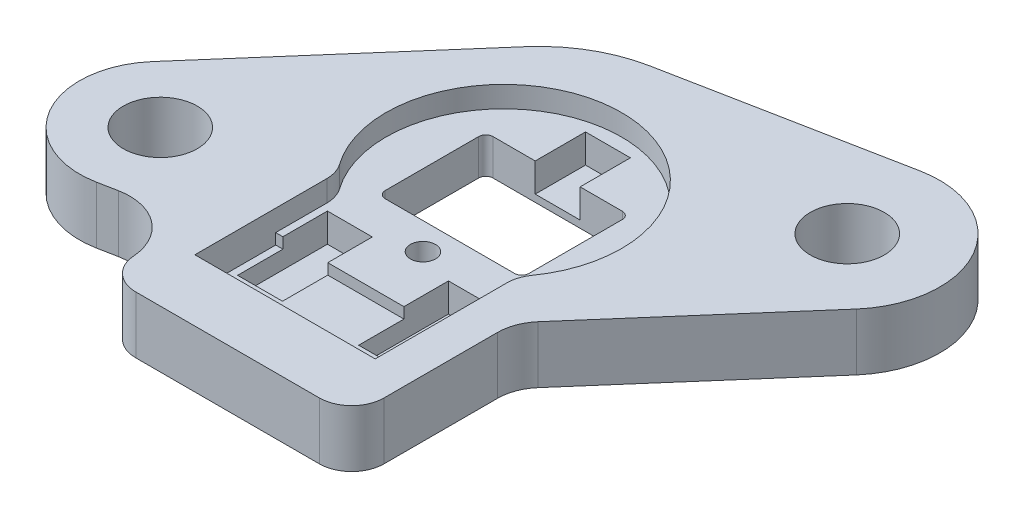
SolidWorks part; units mm, degrees
ref_plane "Front Plane" through (0, 0, 0) normal (0, 0, 1) x (1, 0, 0)
ref_plane "Top Plane" through (0, 0, 0) normal (0, 1, 0) x (1, 0, 0)
ref_plane "Right Plane" through (0, 0, 0) normal (1, 0, 0) x (0, 0, -1)
ref_plane "Plane1" through (0, 2.0193, 0) normal (0, 1, 0) x (1, 0, 0)
sketch "Sketch1" plane through (0, 2.0193, 0) normal (0, 1, 0) x (1, 0, 0)
  line L0 (-8.9344, -19.8323) -> (9.0778, -19.8323)
  line L1 (9.0778, -19.8323) -> (9.0778, -8.3278)
  line L2 (9.0778, -8.3278) -> (20.3302, 4.5954)
  line L3 (14.1448, 15.3088) -> (-5.1925, 11.5337)
  line L4 (-5.1925, 11.5337) -> (-19.708, -5.1371)
  line L5 (-14.3029, -14.4991) -> (-12.9956, -14.2439)
  line L6 (15.3979, 8.89) -> (-15.3979, -8.89) construction
  arc A0 (20.3302, 4.5954) -> (14.1448, 15.3088) centre (15.3979, 8.89) ccw
  arc A1 (-19.708, -5.1371) -> (-14.3029, -14.4991) centre (-15.3979, -8.89) ccw
  arc A2 (-12.9956, -14.2439) -> (-8.9344, -19.8323) centre (-12.2656, -17.9833) cw
  dimension "D1" = 35.56
extrude "Boss-Extrude1" add sketch "Sketch1" against normal blind 4.0386
sketch "Sketch2" plane through (0, -2.0193, 0) normal (0, -1, 0) x (1, 0, 0)
  circle A0 centre (15.3979, -8.89) radius 4.7625
  arc A1 (14.1448, -15.3088) -> (20.3302, -4.5954) centre (15.3979, -8.89) ccw construction
extrude "Boss-Extrude2" add sketch "Sketch2" along normal blind 0.508
sketch "Sketch3" plane through (0, -2.0193, 0) normal (0, -1, 0) x (1, 0, 0)
  circle A0 centre (-15.3979, 8.89) radius 4.7625
  arc A1 (-14.3029, 14.4991) -> (-19.708, 5.1371) centre (-15.3979, 8.89) ccw construction
extrude "Boss-Extrude3" add sketch "Sketch3" along normal blind 0.508
sketch "Sketch4" plane through (0, 2.0193, 0) normal (0, 1, 0) x (-1, 0, 0)
  line L0 (6.3754, 5.3631) -> (6.3754, 15.4686)
  line L1 (6.3754, 15.4686) -> (-6.3754, 15.4686)
  line L2 (-6.3754, 15.4686) -> (-6.3754, 5.3631)
  arc A0 (-6.3754, 5.3631) -> (6.3754, 5.3631) centre (0, 0) ccw
extrude "Cut-Extrude1" cut sketch "Sketch4" against normal blind 1.4986
sketch "Sketch5" plane through (0, 0.5207, 0) normal (0, 1, 0) x (-1, 0, 0)
  line L0 (-6.3754, 9.7536) -> (6.3754, 9.7536)
  line L1 (6.3754, 9.7536) -> (6.3754, 15.4686)
  line L2 (6.3754, 15.4686) -> (-6.3754, 15.4686)
  line L3 (-6.3754, 15.4686) -> (-6.3754, 9.7536)
extrude "Cut-Extrude2" cut sketch "Sketch5" against normal blind 0.762
sketch "Sketch6" plane through (0, -0.2413, 0) normal (0, 1, 0) x (-1, 0, 0)
  line L0 (2.6924, 9.7536) -> (5.8674, 9.7536)
  line L1 (5.8674, 9.7536) -> (5.8674, 12.954)
  line L2 (5.8674, 12.954) -> (2.6924, 12.954)
  line L3 (2.6924, 12.954) -> (2.6924, 9.7536)
extrude "Cut-Extrude3" cut sketch "Sketch6" against normal blind 1.27
sketch "Sketch7" plane through (0, -0.2413, 0) normal (0, 1, 0) x (-1, 0, 0)
  line L0 (-5.8674, 12.954) -> (-5.8674, 9.7536)
  line L1 (-5.8674, 9.7536) -> (-2.6924, 9.7536)
  line L2 (-2.6924, 9.7536) -> (-2.6924, 12.954)
  line L3 (-2.6924, 12.954) -> (-5.8674, 12.954)
extrude "Cut-Extrude4" cut sketch "Sketch7" against normal blind 1.27
sketch "Sketch8" plane through (0, 0, 9.7536) normal (0, 0, 1) x (1, 0, 0)
  line L0 (5.8674, 0.5207) -> (2.6924, 0.5207)
  line L1 (2.6924, 0.5207) -> (2.6924, -1.5113)
  line L2 (2.6924, -1.5113) -> (5.8674, -1.5113)
  line L3 (5.8674, -1.5113) -> (5.8674, 0.5207)
extrude "Cut-Extrude5" cut sketch "Sketch8" against normal blind 3.1496
sketch "Sketch9" plane through (0, 0, 9.7536) normal (0, 0, 1) x (1, 0, 0)
  line L0 (-2.6924, 0.5207) -> (-5.8674, 0.5207)
  line L1 (-5.8674, 0.5207) -> (-5.8674, -1.5113)
  line L2 (-5.8674, -1.5113) -> (-2.6924, -1.5113)
  line L3 (-2.6924, -1.5113) -> (-2.6924, 0.5207)
extrude "Cut-Extrude6" cut sketch "Sketch9" against normal blind 3.1496
sketch "Sketch10" plane through (0, -2.0193, 0) normal (0, -1, 0) x (1, 0, 0)
  line L0 (-5.08, 3.81) -> (-5.08, -3.81)
  line L1 (-5.08, -3.81) -> (5.08, -3.81)
  line L2 (5.08, -3.81) -> (5.08, 3.81)
  line L3 (5.08, 3.81) -> (-5.08, 3.81)
extrude "Cut-Extrude7" cut sketch "Sketch10" against normal through all
sketch "Sketch11" plane through (0, 0, -3.81) normal (0, 0, 1) x (1, 0, 0)
  line L0 (1.5875, -1.5113) -> (1.5875, 0.5207)
  line L1 (1.5875, 0.5207) -> (-1.5875, 0.5207)
  line L2 (-1.5875, 0.5207) -> (-1.5875, -1.5113)
  line L3 (-1.5875, -1.5113) -> (1.5875, -1.5113)
extrude "Cut-Extrude8" cut sketch "Sketch11" against normal blind 3.556
hole_wizard "#10 Clearance Hole1" positions "Sketch15" profile "Sketch14" hole size "#10" standard "ANSI Inch"
sketch "Sketch15" plane through (0, -2.5273, 0) normal (0, -1, 0) x (-1, 0, 0)
  line L0 (15.3979, -8.89) -> (-15.3979, 8.89) construction
  arc A0 (-14.1448, 15.3088) -> (-20.3302, 4.5954) centre (-15.3979, 8.89) ccw construction
  point P0 (15.3979, -8.89)
  point P1 (-15.3979, 8.89)
  dimension "D1" = 35.56
  dimension "D2" = 0
sketch "Sketch14" plane through (-15.3979, -2.5273, 8.89) normal (1, 0, 0) x (0, 0, -1)
  line L0 (0, 0) -> (0, 4.5466)
  line L1 (0, 4.5466) -> (2.6162, 4.5466)
  line L2 (2.6162, 4.5466) -> (2.6162, 0)
  line L5 (2.6162, 0) -> (0, 0)
  line L11 (0, -6.35) -> (0, 107.95) construction
  dimension "Thru Hole Dia." = 5.2324
  dimension "Thru Hole Depth" = 4.5466
hole_wizard "#50 (0.07) Diameter Hole1" positions "Sketch17" profile "Sketch16" hole size "#50" standard "ANSI Inch"
sketch "Sketch17" plane through (0, 0.5207, 0) normal (0, 1, 0) x (1, 0, 0)
  point P0 (0, -5.715)
sketch "Sketch16" plane through (0, 0.5207, 5.715) normal (1, 0, 0) x (0, 0, 1)
  line L0 (0, 0) -> (0, 3.048)
  line L1 (0, 3.048) -> (0.889, 3.048)
  line L2 (0.889, 3.048) -> (0.889, 0)
  line L5 (0.889, 0) -> (0, 0)
  line L11 (0, -6.35) -> (0, 107.95) construction
  dimension "Thru Hole Dia." = 1.778
  dimension "Thru Hole Depth" = 3.048
fillet "Fillet1" radius 0.508 4 edges at (-5.08, -0.7493, 3.81) (-5.08, -0.7493, -3.81) (5.08, -0.7493, 3.81) (5.08, -0.7493, -3.81)
fillet "Fillet3" radius 2.286 4 edges at (-8.9344, 0, 19.8323) (6.3754, 1.27, 5.3631) (-6.3754, 1.27, 5.3631) (9.0778, 0, 19.8323)
fillet "Fillet4" radius 3.175 1 edges at (9.0778, 0, 8.3278)
fillet "Fillet5" radius 9.9187 1 edges at (-5.1925, 0, -11.5337)
